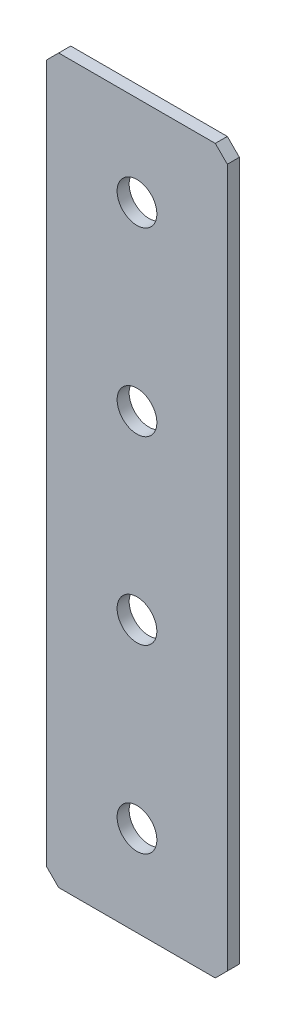
SolidWorks part; units mm, degrees
material "Простая углеродистая сталь"
ref_plane "Спереди(Плоскость XY)" through (0, 0, 0) normal (0, 0, 1) x (1, 0, 0)
ref_plane "Сверху(Плоскость XZ)" through (0, 0, 0) normal (0, 1, 0) x (1, 0, 0)
ref_plane "Справа(Плоскость ZY)" through (0, 0, 0) normal (1, 0, 0) x (0, 0, -1)
sketch "Эскиз1" plane through (0, 0, 0) normal (0, 0, 1) x (1, 0, 0)
  line L1 (-15, -60) -> (15, -60)
  line L2 (-15, -60) -> (-15, 60)
  line L3 (-15, 60) -> (15, 60)
  line L4 (15, -60) -> (15, 60)
  line L5 (-15, -60) -> (15, 60) construction
  line L6 (-15, 60) -> (15, -60) construction
  point P0 (0, 0)
  dimension "D1" = 30
  dimension "D2" = 120
extrude "Бобышка-Вытянуть1" add sketch "Эскиз1" along normal blind 2
chamfer "Фаска1" distance 2 angle 45 4 edges at (-15, -60, 1) (15, -60, 1) (-15, 60, 1) (15, 60, 1)
hole_wizard "Отверстие с зазором M61" positions "Эскиз2" profile "Эскиз3" hole size "M6" standard "DIN" end condition through all
sketch "Эскиз2" plane through (0, 0, 2) normal (0, 0, 1) x (1, 0, 0)
  line L12 (0, 60) -> (0, -60) construction
  line L13 (13, 60) -> (-13, 60) construction
  line L14 (-13, -60) -> (13, -60) construction
  point P204 (0, 45)
  point P206 (0, 15)
  point P208 (0, -15)
  point P210 (0, -45)
  dimension "D1" = 30
  dimension "D2" = 30
  dimension "D3" = 30
  dimension "D4" = 15
sketch "Эскиз3" plane through (0, -45, 2) normal (1, 0, 0) x (0, -1, 0)
  line L0 (0, 0) -> (0, 2)
  line L1 (0, 2) -> (3.3, 2)
  line L2 (3.3, 2) -> (3.3, 0)
  line L5 (3.3, 0) -> (0, 0)
  line L11 (0, -6.35) -> (0, 107.95) construction
  dimension "Диаметр сквозного отверстия" = 6.6
  dimension "Глубина сквозного отверстия" = 2
